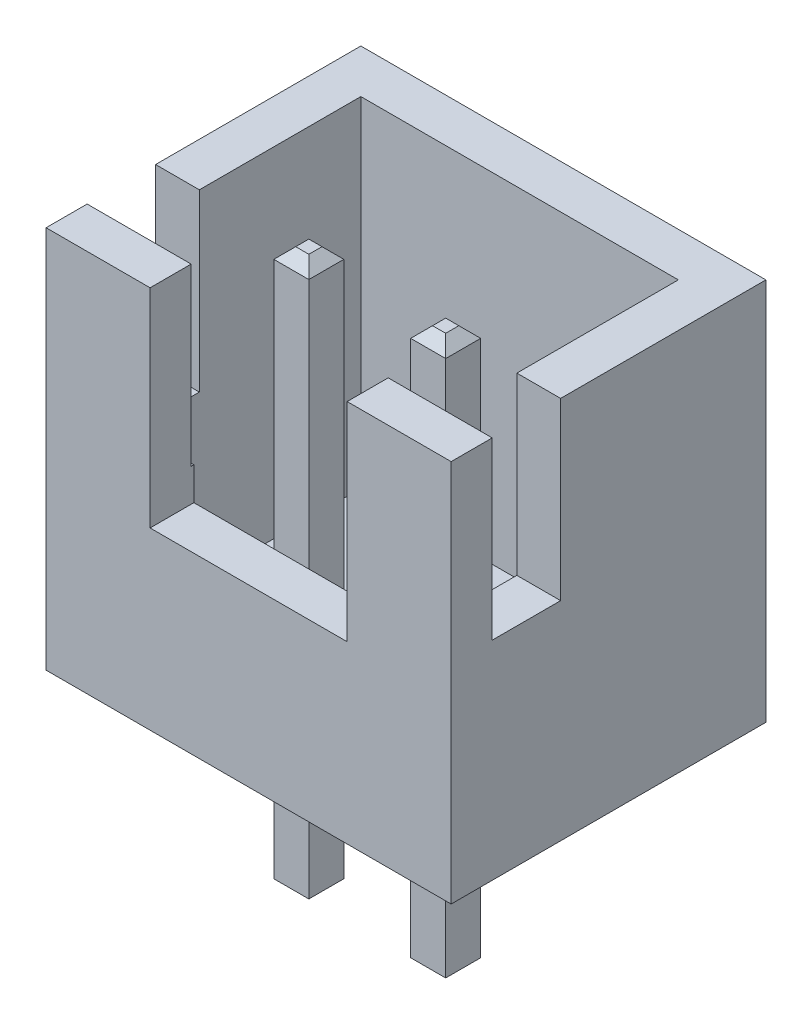
SolidWorks part; units mm, degrees
other "Camera1"
ref_plane "Front Plane" through (0, 0, 0) normal (0, 0, 1) x (1, 0, 0)
ref_plane "Top Plane" through (0, 0, 0) normal (0, 1, 0) x (1, 0, 0)
ref_plane "Right Plane" through (0, 0, 0) normal (1, 0, 0) x (0, 0, -1)
sketch "Sketch1" plane through (0, 0, 0) normal (0, 1, 0) x (1, 0, 0)
  line L1 (-3.7, 2.875) -> (3.7, 2.875)
  line L2 (-3.7, 2.875) -> (-3.7, -2.875)
  line L3 (-3.7, -2.875) -> (3.7, -2.875)
  line L4 (3.7, 2.875) -> (3.7, -2.875)
  line L5 (-3.7, 2.875) -> (3.7, -2.875) construction
  line L6 (-3.7, -2.875) -> (3.7, 2.875) construction
  point P0 (0, 0)
  dimension "D1" = 5.75
  dimension "D2" = 7.4
extrude "Boss-Extrude1" add sketch "Sketch1" along normal blind 7
shell "Shell1" thickness 0.8
sketch "Sketch2" plane through (3.7, 0, 0) normal (1, 0, 0) x (0, 0, -1)
  line L0 (-0.875, 7) -> (-0.875, 3.8)
  line L1 (-2.875, 7) -> (2.875, 7) construction
  line L2 (-2.125, 3.8) -> (-2.125, 7)
  line L3 (-2.125, 7) -> (-0.875, 7)
  line L4 (-2.875, 7) -> (-2.875, 0) construction
  line L5 (-0.875, 3.8) -> (-2.125, 3.8)
  dimension "D1" = 0.75
  dimension "D2" = 1.25
  dimension "D3" = 3.2
extrude "Cut-Extrude1" cut sketch "Sketch2" against normal through all
sketch "Sketch3" plane through (0, 0, 2.875) normal (0, 0, 1) x (1, 0, 0)
  line L0 (-1.8, 7) -> (-1.8, 3.2)
  line L1 (-3.7, 7) -> (3.7, 7) construction
  line L2 (-3.7, 7) -> (-3.7, 0) construction
  line L3 (1.8, 3.2) -> (-1.8, 3.2)
  line L6 (1.8, 7) -> (-1.8, 7)
  line L8 (0, 7) -> (0, 0) construction
  line L14 (1.8, 7) -> (1.8, 3.2)
  dimension "D1" = 1.9
  dimension "D3" = 3.8
extrude "Cut-Extrude2" cut sketch "Sketch3" against normal up to next
sketch "Sketch4" plane through (0, 0, 0) normal (0, -1, 0) x (1, 0, 0)
  line L1 (-1.57, 0.845) -> (-0.93, 0.845)
  line L2 (-1.57, 0.845) -> (-1.57, 0.205)
  line L3 (-1.57, 0.205) -> (-0.93, 0.205)
  line L4 (-0.93, 0.845) -> (-0.93, 0.205)
  line L5 (-1.57, 0.845) -> (-0.93, 0.205) construction
  line L6 (-1.57, 0.205) -> (-0.93, 0.845) construction
  line L7 (0, 1.9141) -> (0, 0) construction
  line L8 (0, 0) -> (2.4975, 0) construction
  line L9 (-3.7, 2.875) -> (3.7, 2.875) construction
  line L10 (0.93, 0.845) -> (0.93, 0.205)
  line L11 (1.57, 0.205) -> (0.93, 0.205)
  line L12 (1.57, 0.845) -> (1.57, 0.205)
  line L13 (1.57, 0.845) -> (0.93, 0.845)
  point P0 (-1.25, 0.525)
  dimension "D1" = 0.64
  dimension "D2" = 0.64
  dimension "D3" = 2.5
  dimension "D4" = 2.35
extrude "Boss-Extrude2" add sketch "Sketch4" along normal blind 3.45 and the other way blind 6.75
chamfer "Chamfer1" distance 0.2 angle 45 16 edges at (-1.25, -3.45, 0.205) (-1.57, -3.45, 0.525) (-1.25, -3.45, 0.845) (-0.93, -3.45, 0.525) (-1.25, 6.75, 0.845) (-1.57, 6.75, 0.525) (-1.25, 6.75, 0.205) (-0.93, 6.75, 0.525) (0.93, 6.75, 0.525) (1.25, 6.75, 0.205) (1.57, 6.75, 0.525) (1.25, 6.75, 0.845) (1.57, -3.45, 0.525) (1.25, -3.45, 0.205) (0.93, -3.45, 0.525) (1.25, -3.45, 0.845)
